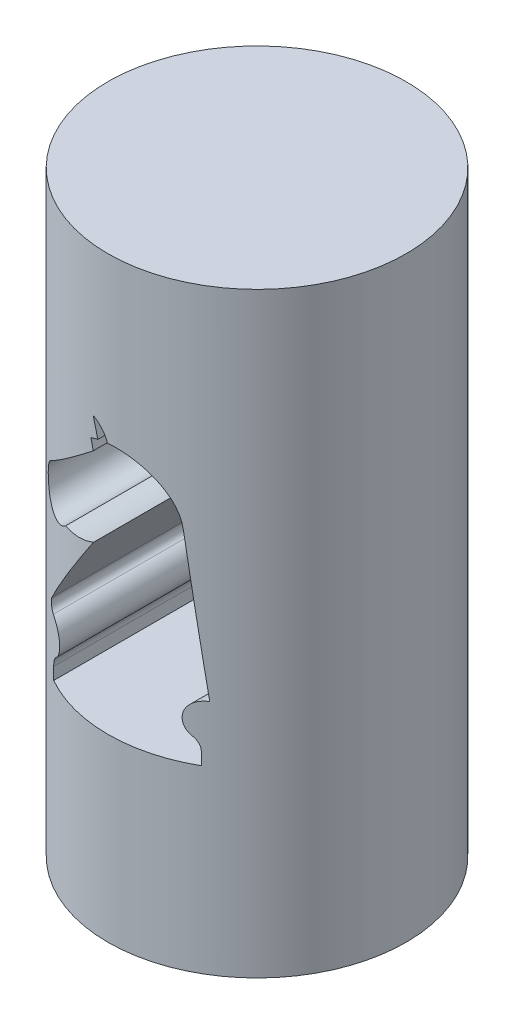
SolidWorks part; units mm, degrees
ref_plane "Front" through (0, 0, 0) normal (0, 0, 1) x (1, 0, 0)
ref_plane "Top" through (0, 0, 0) normal (0, 1, 0) x (1, 0, 0)
ref_plane "Right" through (0, 0, 0) normal (1, 0, 0) x (0, 0, -1)
sketch "Sketch2" plane through (0, 0, 0) normal (0, 1, 0) x (1, 0, 0)
  circle A0 centre (0, 0) radius 10
  dimension "D1" = 20
extrude "Boss-Extrude1" add sketch "Sketch2" along normal mid plane 40
sketch "Sketch3" plane through (0, 0, 0) normal (0, 0, 1) x (1, 0, 0)
  line L0 (-4.95, -7.92) -> (4.95, -7.92)
  line L1 (4.95, -7.92) -> (4.95, -7.095)
  line L2 (-4.95, -7.095) -> (-4.95, -7.92)
  line L11 (5.3039, -4.1187) -> (4.1526, 5.5959)
  line L12 (-1.0434, 8.0006) -> (-5.4537, 4.4564)
  line L14 (-1.0292, 2.6933) -> (-5.2626, -3.3529)
  line L15 (-1.2124, 8.6716) -> (-1.0434, 8.0006)
  line L16 (-0.7048, 8.8521) -> (-1.0434, 10.0674)
  arc A0 (4.95, -7.095) -> (4.5529, -6.2728) centre (3.9003, -7.095) ccw
  arc A4 (-4.5802, -6.2953) -> (-4.95, -7.095) centre (-3.9003, -7.095) ccw
  arc A6 (-5.0075, -4.1187) -> (-4.5802, -6.2953) centre (-5.4036, -5.3267) cw
  arc A8 (5.3039, -4.1187) -> (4.5529, -6.2728) centre (5.3039, -5.3267) ccw
  arc A23 (-5.4537, 4.4564) -> (-3.4393, 2.1729) centre (-4.499, 3.2683) ccw
  arc A24 (-3.4393, 2.1729) -> (-1.0292, 2.6933) centre (-3.4364, 8.0006) ccw
  arc A25 (-5.2626, -3.3529) -> (-5.0075, -4.1187) centre (-4.8509, -3.6411) ccw
  arc A26 (4.1526, 5.5959) -> (-0.033, 8.9764) centre (0.3287, 5.1428) ccw
  arc A27 (-0.7048, 8.8521) -> (-1.2124, 8.6716) centre (0.3287, 5.1428) ccw
  arc A28 (-1.0434, 10.0674) -> (-0.033, 8.9764) centre (-1.7402, 8.4087) cw
extrude "Cut-Extrude1" cut sketch "Sketch3" against normal through all both and the other way through all
sketch "Sketch4" plane through (0, -20, 0) normal (0, -1, 0) x (-1, 0, 0)
  circle A0 centre (0, 0) radius 3
  dimension "D1" = 6
extrude "Cut-Extrude2" cut sketch "Sketch4" against normal blind 3
